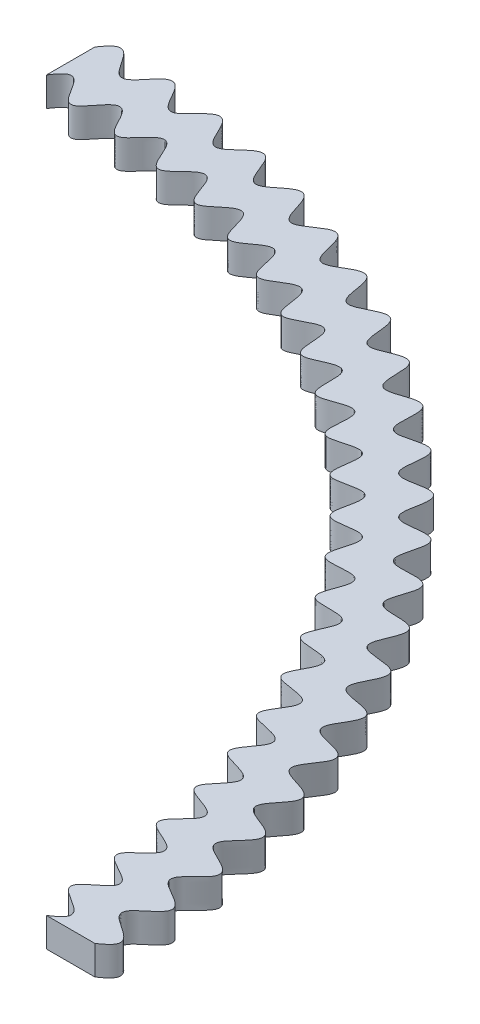
SolidWorks part; units mm, degrees
ref_plane "Front Plane" through (0, 0, 0) normal (0, 0, 1) x (1, 0, 0)
ref_plane "Top Plane" through (0, 0, 0) normal (0, 1, 0) x (1, 0, 0)
ref_plane "Right Plane" through (0, 0, 0) normal (1, 0, 0) x (0, 0, -1)
sketch "Sketch1" plane through (0, 0, 0) normal (0, 1, 0) x (1, 0, 0)
  line L0 (0, 75) -> (0, 80)
  line L1 (75, 0) -> (80, 0)
  spline S0 degree 4 number of poles 687 (78.7091, -11.4049) -> (-11.4049, 78.7091) construction
  spline S1 degree 4 number of poles 577 (80, 0) -> (0, 80)
  spline S2 degree 4 number of poles 721 (73.8501, -10.6424) -> (-10.6424, 73.8501) construction
  spline S3 degree 4 number of poles 612 (75, 0) -> (0, 75)
extrude "Boss-Extrude1" add sketch "Sketch1" along normal blind 3 contours S3 L0 S1 L1
